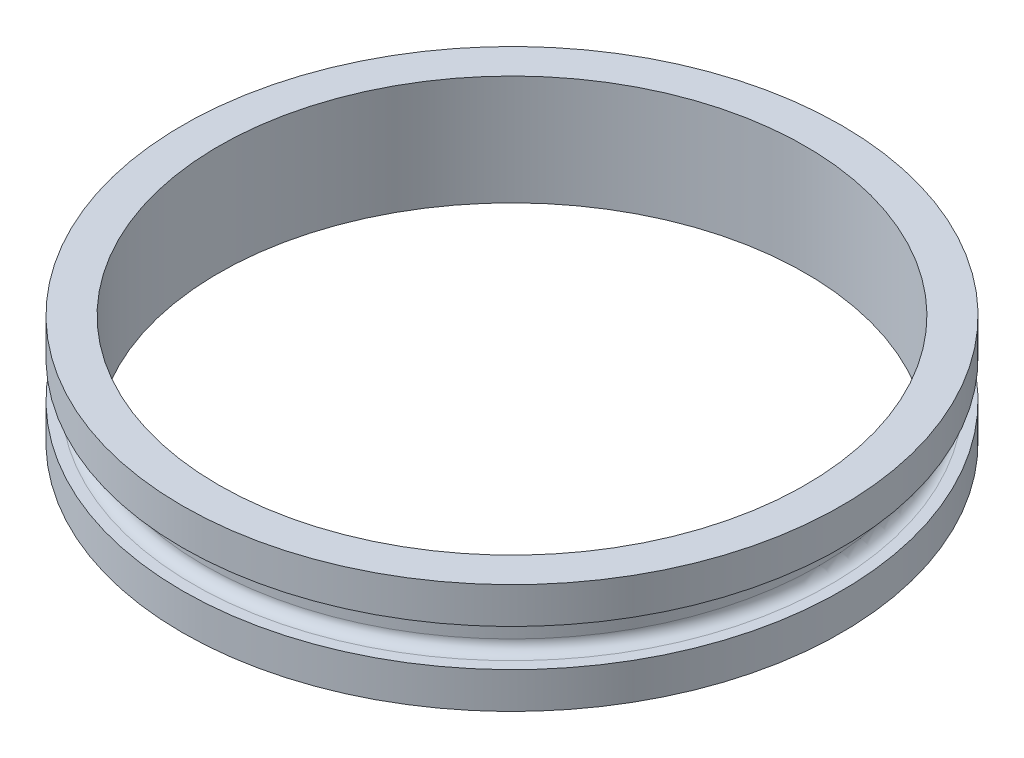
SolidWorks part; units mm, degrees
material "PLA"
ref_plane "Front Plane" through (0, 0, 0) normal (0, 0, 1) x (1, 0, 0)
ref_plane "Top Plane" through (0, 0, 0) normal (0, 1, 0) x (1, 0, 0)
ref_plane "Right Plane" through (0, 0, 0) normal (1, 0, 0) x (0, 0, -1)
sketch "Sketch1" plane through (0, 0, 0) normal (0, 0, 1) x (1, 0, 0)
  line L0 (33.9217, 0) -> (33.9217, 12.7)
  line L1 (33.9217, 12.7) -> (38.1, 12.7)
  line L2 (38.1, 12.7) -> (38.1, 8.509)
  line L3 (38.1, 8.509) -> (35.56, 8.509)
  line L4 (35.56, 8.509) -> (35.56, 4.191)
  line L5 (35.56, 4.191) -> (38.1, 4.191)
  line L6 (38.1, 4.191) -> (38.1, 0)
  line L7 (38.1, 0) -> (33.9217, 0)
  dimension "D2" = 4.318
  dimension "D3" = 12.7
  dimension "D4" = 4.191
  dimension "D5" = 2.54
  dimension "D6" = 1.6383
  dimension "D1" = 38.1
ref_axis "Axis1" through (0, 13.335, 0) along (0, -1, 0)
revolve "Revolve1" add sketch "Sketch1" angle 360 about axis through (0, 13.335, 0) along (0, -1, 0)
fillet "Fillet1" radius 1.27 2 edges at (0, 4.191, 35.56) (0, 8.509, 35.56)
equation "\"D1@Sketch1\"=(3.01-\"tolerance_body tube\")/2"
equation "\"tolerance_body tube\"= 0.01"
